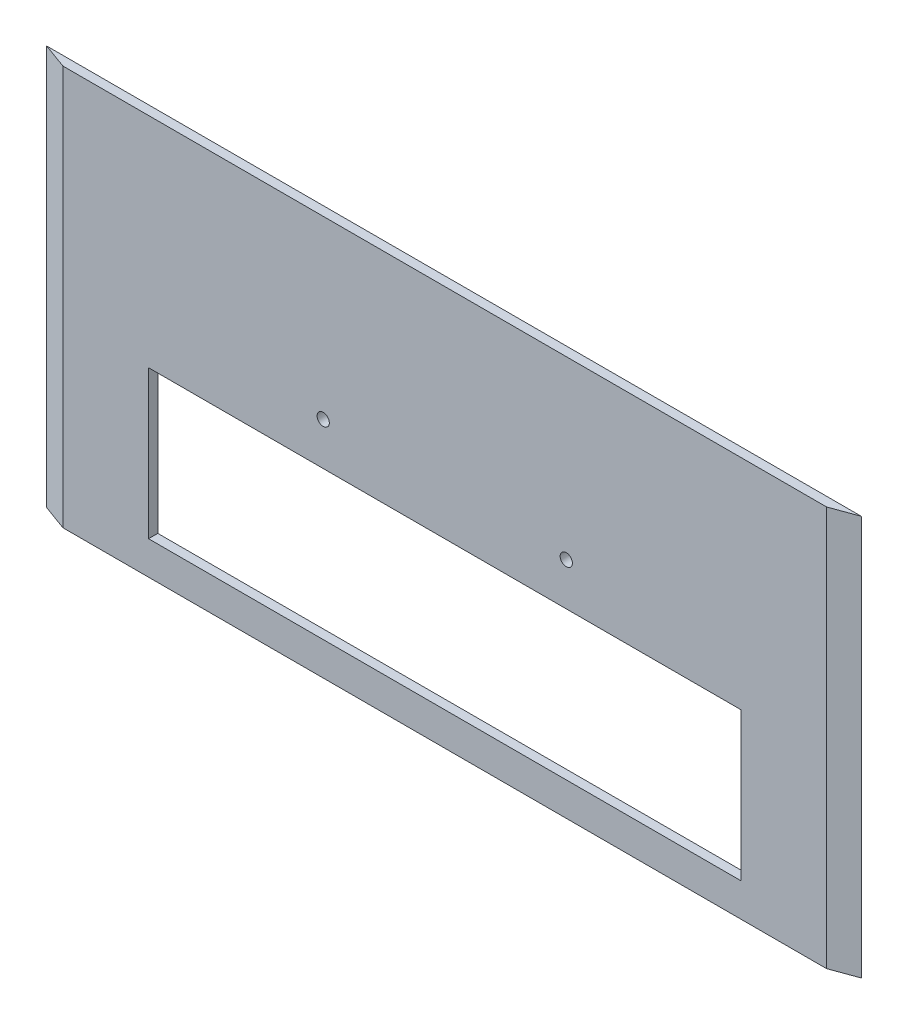
SolidWorks part; units mm, degrees
ref_plane "Front Plane" through (0, 0, 0) normal (0, 0, 1) x (1, 0, 0)
ref_plane "Top Plane" through (0, 0, 0) normal (0, 1, 0) x (1, 0, 0)
ref_plane "Right Plane" through (0, 0, 0) normal (1, 0, 0) x (0, 0, -1)
sketch "Sketch1" plane through (0, 0, 0) normal (0, 0, 1) x (1, 0, 0)
  line L1 (-87.5, -31.5) -> (87.5, -31.5)
  line L2 (-87.5, -31.5) -> (-87.5, 31.5)
  line L3 (-87.5, 31.5) -> (87.5, 31.5)
  line L4 (87.5, -31.5) -> (87.5, 31.5)
  line L5 (-87.5, -31.5) -> (87.5, 31.5) construction
  line L6 (-87.5, 31.5) -> (87.5, -31.5) construction
  point P0 (0, 0)
  dimension "D1" = 63
  dimension "D2" = 175
extrude "Boss-Extrude1" add sketch "Sketch1" along normal blind 2.5
sketch "Sketch2" plane through (0, 0, 2.5) normal (0, 0, 1) x (1, 0, 0)
  line L1 (-80, -22.5) -> (80, -22.5)
  line L2 (-80, -22.5) -> (-80, 17.5)
  line L3 (-80, 17.5) -> (80, 17.5)
  line L4 (80, -22.5) -> (80, 17.5)
  line L5 (-80, -22.5) -> (80, 17.5) construction
  line L6 (-80, 17.5) -> (80, -22.5) construction
  point P0 (0, -2.5)
  dimension "D1" = 40
  dimension "D2" = 160
  dimension "D3" = 2.5
extrude "Cut-Extrude1" cut sketch "Sketch2" against normal blind 2.5
sketch "Sketch5" plane through (0, 0, 2.5) normal (0, 0, 1) x (1, 0, 0)
  line L0 (87.5, 31.5) -> (-87.5, 31.5) construction
  line L1 (-87.5, 31.5) -> (87.5, 31.5)
  line L2 (-87.5, 31.5) -> (-87.5, 76.5)
  line L3 (-87.5, 76.5) -> (87.5, 76.5)
  line L4 (87.5, 31.5) -> (87.5, 76.5)
  dimension "D1" = 45
extrude "Boss-Extrude3" add sketch "Sketch5" against normal up to surface (2.5 mm away) up to face at (0, -2.5, 0)
sketch "Sketch3" plane through (0, -31.5, 0) normal (0, 1, 0) x (1, 0, 0)
  line L0 (-87.5, -2.5) -> (-103.1313, -2.5)
  line L1 (-103.1313, -2.5) -> (-110, 0)
  line L2 (-110, 0) -> (-87.5, 0)
  line L3 (-87.5, 0) -> (-87.5, -2.5)
  line L5 (-87.5, 0) -> (87.5, 0) construction
  dimension "D1" = 22.5
  dimension "D2" = 20
extrude "Boss-Extrude2" add sketch "Sketch3" along normal up to surface (108 mm away) up to face at (0, 76.5, 1.25)
mirror "Mirror1" about plane through (0, 0, 0) normal (1, 0, 0) of "Boss-Extrude2"
sketch "Sketch4" plane through (0, 0, 0) normal (0, 0, -1) x (-1, 0, 0)
  circle A3 centre (-32.825, 29) radius 1.65
  arc A4 (-32.825, 27.35) -> (-32.825, 30.65) centre (-32.825, 29) ccw construction
  point P2 (-57.4156, 28.8986)
  point P4 (-34.325, 29)
extrude "Cut-Extrude2" cut sketch "Sketch4" against normal through all
mirror "Mirror2" about plane through (0, 0, 0) normal (1, 0, 0) of "Cut-Extrude2"
